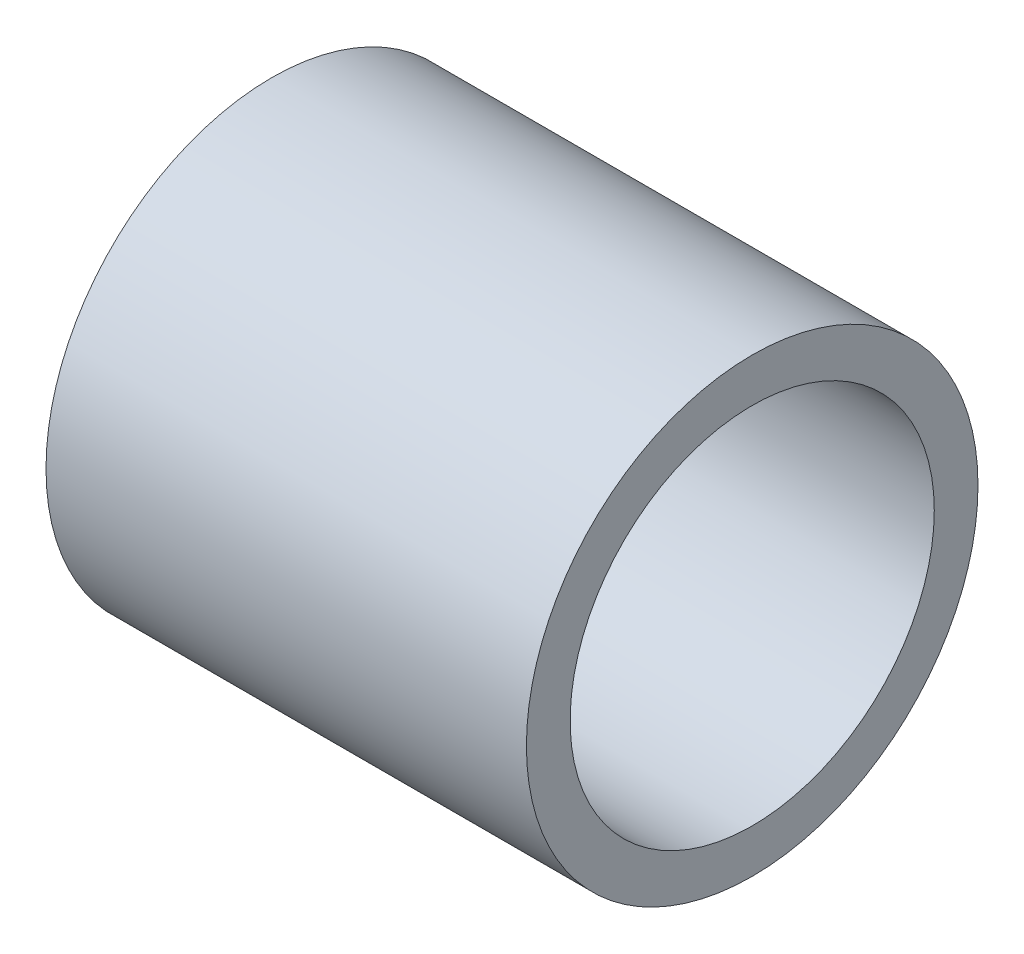
SolidWorks part; units mm, degrees
ref_plane "Front Plane" through (0, 0, 0) normal (0, 0, 1) x (1, 0, 0)
ref_plane "Top Plane" through (0, 0, 0) normal (0, 1, 0) x (1, 0, 0)
ref_plane "Right Plane" through (0, 0, 0) normal (1, 0, 0) x (0, 0, -1)
sketch "Sketch1" plane through (0, 0, 0) normal (1, 0, 0) x (0, 0, -1)
  circle A0 centre (0, 0) radius 5.969 construction
  circle A1 centre (0, 0) radius 4.8133 construction
  dimension "ID" = 9.6266
  dimension "OD" = 11.938
sketch "Sketch2" plane through (0, 0, 0) normal (0, 0, 1) x (1, 0, 0)
  line L0 (-6.35, 5.969) -> (6.35, 5.969) construction
  point P4 (0, 5.969)
  dimension "Length" = 12.7
sketch "Sketch3" plane through (0, 0, 0) normal (1, 0, 0) x (0, 0, -1)
  circle A0 centre (0, 0) radius 5.969
  circle A1 centre (0, 0) radius 4.8133
  circle A2 centre (0, 0) radius 4.8133 construction
extrude "Boss-Extrude1" add sketch "Sketch3" along normal up to vertex (6.35 mm away) and the other way up to vertex (6.35 mm away) up to point (6.35, 5.969, 0) other way up to point (-6.35, 5.969, 0)
